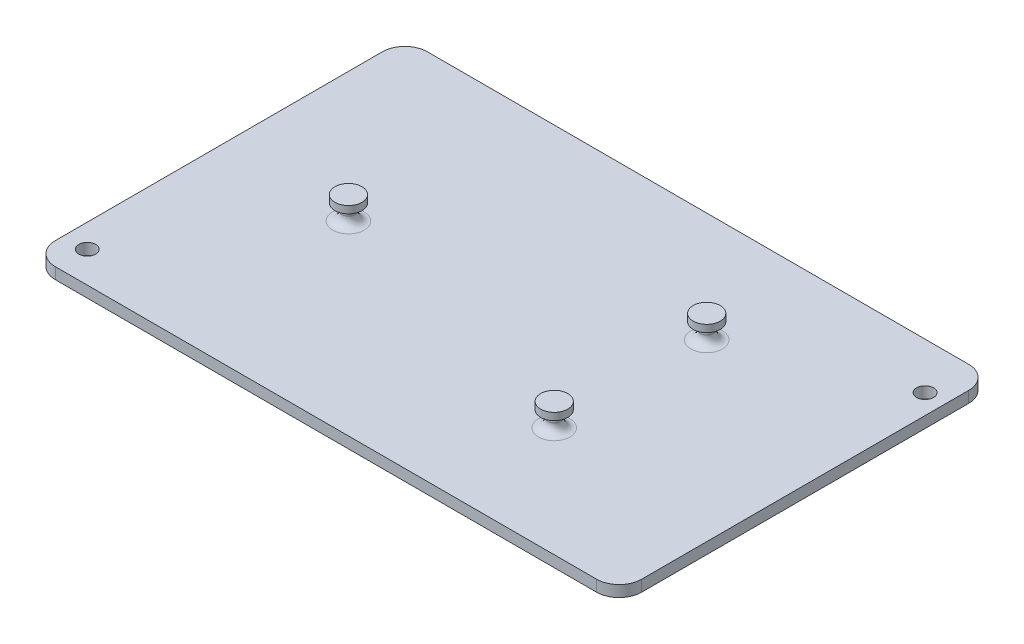
SolidWorks part; units mm, degrees
ref_plane "Front Plane" through (0, 0, 0) normal (0, 0, 1) x (1, 0, 0)
ref_plane "Top Plane" through (0, 0, 0) normal (0, 1, 0) x (1, 0, 0)
ref_plane "Right Plane" through (0, 0, 0) normal (1, 0, 0) x (0, 0, -1)
sketch "Sketch1" plane through (0, 0, 0) normal (0, 1, 0) x (1, 0, 0)
  line L1 (-82.55, -52.3875) -> (82.55, -52.3875)
  line L2 (-82.55, -52.3875) -> (-82.55, 52.3875)
  line L3 (-82.55, 52.3875) -> (82.55, 52.3875)
  line L4 (82.55, -52.3875) -> (82.55, 52.3875)
  line L5 (-82.55, -52.3875) -> (82.55, 52.3875) construction
  line L6 (-82.55, 52.3875) -> (82.55, -52.3875) construction
  point P0 (0, 0)
  dimension "D1" = 165.1
  dimension "D2" = 104.775
extrude "Boss-Extrude1" add sketch "Sketch1" along normal blind 3.175
sketch "Sketch2" plane through (0, 0, 0) normal (0, 0, 1) x (1, 0, 0)
  line L0 (-46.0502, 3.175) -> (-46.0502, 9.652)
  line L1 (-82.55, 3.175) -> (82.55, 3.175) construction
  line L2 (-46.0502, 9.652) -> (-42.2402, 9.652)
  line L3 (-42.2402, 9.652) -> (-42.2402, 7.62)
  line L4 (-42.2402, 7.62) -> (-44.1452, 7.62)
  line L5 (-44.1452, 7.62) -> (-44.1452, 3.175)
  line L6 (-46.0502, 3.175) -> (-44.1452, 3.175)
  dimension "D1" = 3.81
  dimension "D2" = 2.032
  dimension "D3" = 6.477
  dimension "D4" = 46.0502
  dimension "D5" = 1.905
revolve "Revolve1" add sketch "Sketch2" angle 360 about L0
ref_plane "Plane1" through (33.3502, 0, 0) normal (1, 0, 0) x (0, 0, -1)
sketch "Sketch3" plane through (33.3502, 0, 0) normal (1, 0, 0) x (0, 0, -1)
  line L0 (-21.463, 3.175) -> (-21.463, 9.652)
  line L1 (-52.3875, 3.175) -> (52.3875, 3.175) construction
  line L2 (-21.463, 9.652) -> (-17.653, 9.652)
  line L3 (-17.653, 9.652) -> (-17.653, 7.62)
  line L4 (-17.653, 7.62) -> (-19.558, 7.62)
  line L5 (-19.558, 7.62) -> (-19.558, 3.175)
  line L6 (-19.558, 3.175) -> (-21.463, 3.175)
  dimension "D1" = 21.463
  dimension "D2" = 1.905
  dimension "D3" = 3.81
  dimension "D4" = 6.477
  dimension "D5" = 2.032
revolve "Revolve2" add sketch "Sketch3" angle 360 about L0
mirror "Mirror1" about plane through (0, 0, 0) normal (0, 0, 1) of "Revolve2"
fillet "Fillet1" radius 2.54 3 edges at (33.3502, 3.175, -19.558) (33.3502, 3.175, 19.558) (-46.0502, 3.175, -1.905)
fillet "Fillet2" radius 0.508 3 edges at (33.3502, 7.62, -19.558) (33.3502, 7.62, 19.558) (-46.0502, 7.62, -1.905)
fillet "Fillet3" radius 6.35 4 edges at (-82.55, 1.5875, -52.3875) (-82.55, 1.5875, 52.3875) (82.55, 1.5875, -52.3875) (82.55, 1.5875, 52.3875)
sketch "Sketch4" plane through (0, 3.175, 0) normal (0, 1, 0) x (1, 0, 0)
  line L0 (-76.2, -52.3875) -> (76.2, -52.3875) construction
  line L1 (-82.55, 46.0375) -> (-82.55, -46.0375) construction
  line L2 (82.55, -46.0375) -> (82.55, 46.0375) construction
  line L3 (76.2, 52.3875) -> (-76.2, 52.3875) construction
  circle A0 centre (-75.933, -43.6435) radius 2.3813
  circle A1 centre (76.967, 39.3345) radius 2.3813
  dimension "D1" = 4.7625
  dimension "D2" = 8.744
  dimension "D3" = 6.617
  dimension "D4" = 5.583
  dimension "D5" = 13.053
extrude "Cut-Extrude1" cut sketch "Sketch4" against normal through all
